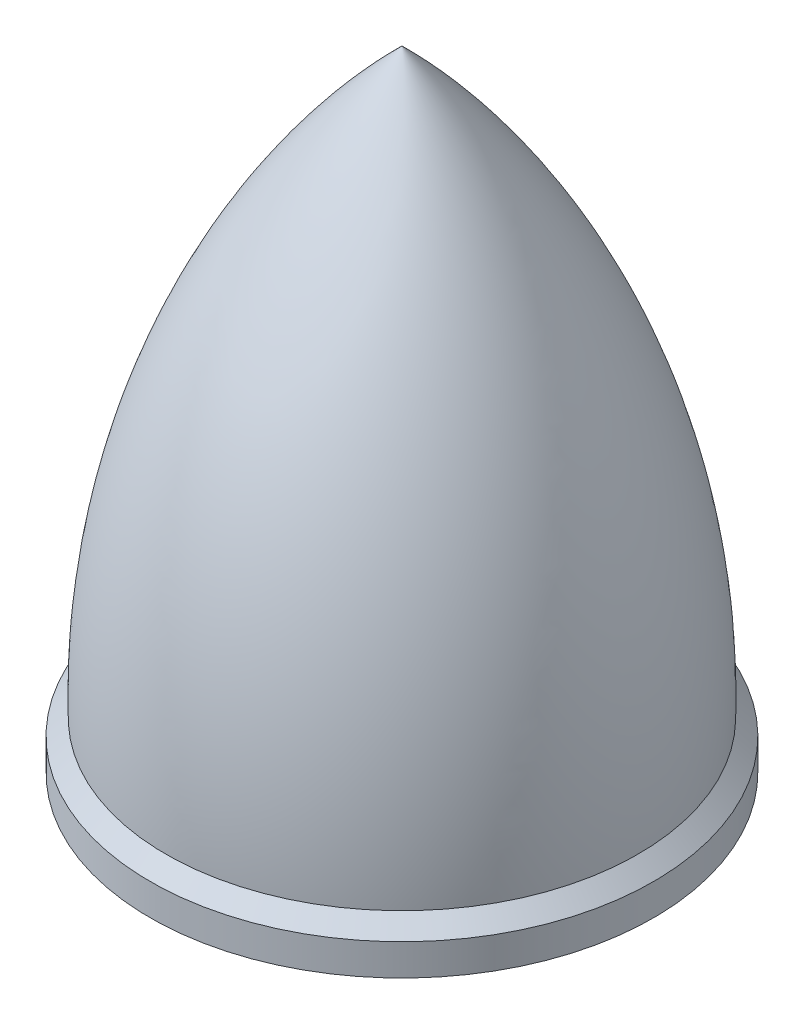
SolidWorks part; units mm, degrees
ref_plane "Front" through (0, 0, 0) normal (0, 0, 1) x (1, 0, 0)
ref_plane "Top" through (0, 0, 0) normal (0, 1, 0) x (1, 0, 0)
ref_plane "Right" through (0, 0, 0) normal (1, 0, 0) x (0, 0, -1)
sketch "Sketch2" plane through (0, 0, 0) normal (0, 0, 1) x (1, 0, 0)
  line L0 (0, 0) -> (8, 0)
  line L2 (8, 0) -> (8, 1)
  line L3 (8, 1) -> (7.5, 1.5)
  line L5 (0, 0) -> (0, 20)
  arc A0 (7.5, 1.5) -> (0, 20) centre (-17.4918, 2.1384) ccw
  dimension "D6" = 25
  dimension "D1" = 8
  dimension "D2" = 1
  dimension "D3" = 20
  dimension "D4" = 45
  dimension "D5" = 0.5
revolve "Revolve1" add sketch "Sketch2" angle 360 about L5
hole_wizard "Ø5.0 (5) Diameter Hole1" positions "Sketch4" profile "Sketch3" hole size "Ø5.0" standard "ANSI Metric"
sketch "Sketch4" plane through (0, 0, 0) normal (0, -1, 0) x (-1, 0, 0)
  point P0 (0, 0)
sketch "Sketch3" plane through (0, 0, 0) normal (1, 0, 0) x (0, 0, -1)
  line L0 (0, 0) -> (0, 11.5022)
  line L1 (0, 11.5022) -> (2.5, 10)
  line L2 (2.5, 10) -> (2.5, 0)
  line L5 (2.5, 0) -> (0, 0)
  line L10 (0, 11.5022) -> (-2.5, 10) construction
  line L11 (0, -6.35) -> (0, 107.95) construction
  dimension "Hole Dia." = 5
  dimension "Hole Depth" = 10
  dimension "Drill Angle" = 118
